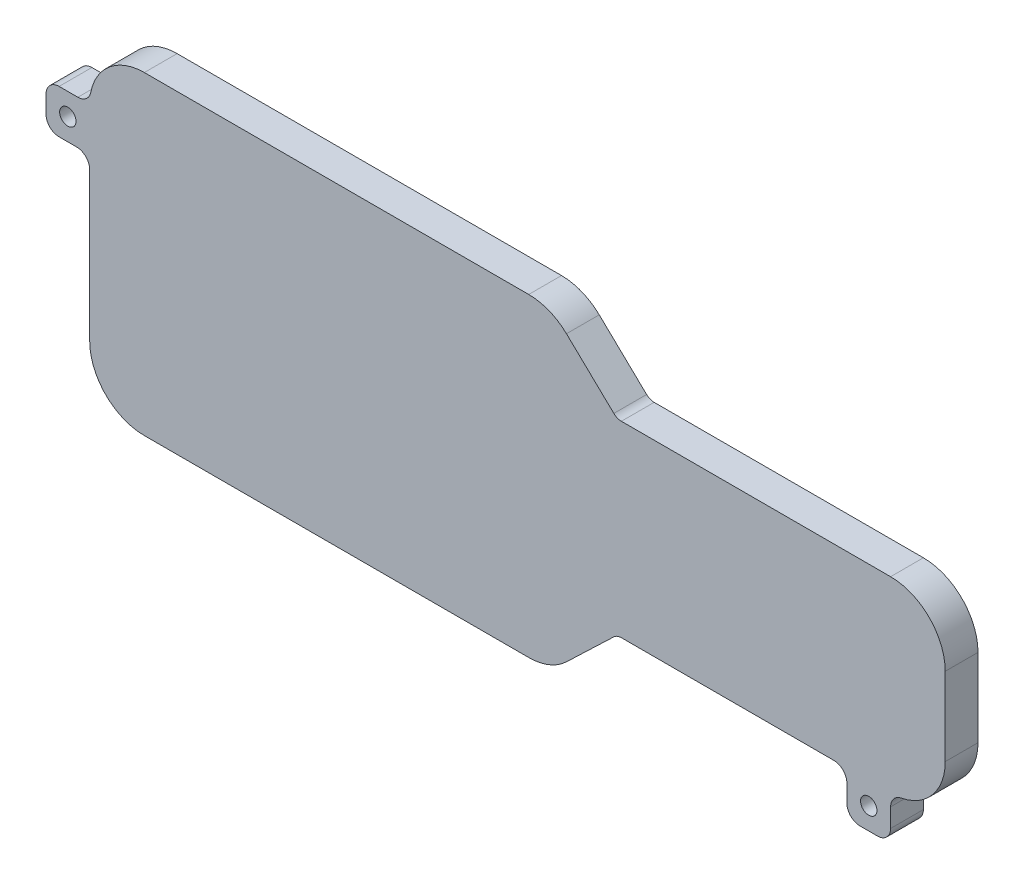
SolidWorks part; units mm, degrees
ref_plane "Front Plane" through (0, 0, 0) normal (0, 0, 1) x (1, 0, 0)
ref_plane "Top Plane" through (0, 0, 0) normal (0, 1, 0) x (1, 0, 0)
ref_plane "Right Plane" through (0, 0, 0) normal (1, 0, 0) x (0, 0, -1)
sketch "Sketch2" plane through (0, 0, 0) normal (0, 0, 1) x (1, 0, 0)
  line L0 (-34.29, 10.16) -> (0, 10.16)
  line L1 (-34.29, 10.16) -> (-34.29, 0)
  line L2 (-34.29, 0) -> (0, 0)
  line L3 (0, 10.16) -> (0, 0)
  line L4 (-69.31, 13.97) -> (-36.29, 13.97)
  line L5 (-69.31, 13.97) -> (-69.31, -3.81)
  line L6 (-69.31, -3.81) -> (-36.29, -3.81)
  line L7 (-36.29, 13.97) -> (-36.29, -3.81)
  line L8 (-31.29, 10.16) -> (-31.29, 0)
  line L9 (-71.31, 15.97) -> (-34.29, 15.97)
  line L10 (-34.29, 15.97) -> (-34.29, 12.16)
  line L11 (-34.29, 12.16) -> (-31.29, 12.16)
  line L12 (-31.29, 12.16) -> (-31.29, -2)
  line L13 (-31.29, -2) -> (-34.29, -2)
  line L14 (-34.29, -2) -> (-34.29, -5.81)
  line L15 (-34.29, -5.81) -> (-71.31, -5.81)
  line L16 (-71.31, -5.81) -> (-71.31, 15.97)
  point P4 (-34.29, 5.08)
  point P5 (-36.29, 5.08)
  dimension "D1" = 2
  dimension "D2" = 2
  dimension "D3" = 2
  dimension "D5" = 2
  dimension "D4" = 2
  dimension "D6" = 0
sketch "Sketch3" plane through (0, 0, 0) normal (0, 0, 1) x (1, 0, 0)
  line L0 (-69.81, 17.47) -> (-34.6251, 17.47)
  line L1 (-32.5518, 16.6383) -> (-28.2152, 12.4917)
  line L2 (-26.1419, 11.66) -> (-1.5, 11.66)
  line L3 (1.5, 8.66) -> (1.5, 1.5)
  line L4 (-1.5, -1.5) -> (-26.1419, -1.5)
  line L5 (-28.2152, -2.3317) -> (-32.5518, -6.4783)
  line L6 (-34.6251, -7.31) -> (-69.81, -7.31)
  line L7 (-72.81, -4.31) -> (-72.81, 14.47)
  line L8 (-71.31, 15.97) -> (-34.29, 15.97) construction
  line L9 (-34.29, -5.81) -> (-71.31, -5.81) construction
  line L11 (-34.29, 0) -> (0, 0) construction
  line L12 (0, 10.16) -> (0, 0) construction
  line L13 (-71.31, -5.81) -> (-71.31, 15.97) construction
  line L14 (-69.81, 19.47) -> (-34.6251, 19.47)
  line L15 (-31.1696, 18.0838) -> (-26.833, 13.9372)
  line L16 (-26.1419, 13.66) -> (-1.5, 13.66)
  line L17 (3.5, 8.66) -> (3.5, 1.5)
  line L18 (-1.5, -3.5) -> (-26.1419, -3.5)
  line L19 (-26.833, -3.7772) -> (-31.1696, -7.9238)
  line L20 (-34.6251, -9.31) -> (-69.81, -9.31)
  line L21 (-74.81, -4.31) -> (-74.81, 14.47)
  arc A0 (-69.81, -7.31) -> (-72.81, -4.31) centre (-69.81, -4.31) cw
  arc A1 (-1.5, 11.66) -> (1.5, 8.66) centre (-1.5, 8.66) cw
  arc A2 (1.5, 1.5) -> (-1.5, -1.5) centre (-1.5, 1.5) cw
  arc A3 (-32.5518, -6.4783) -> (-34.6251, -7.31) centre (-34.6251, -4.31) cw
  arc A4 (-26.1419, -1.5) -> (-28.2152, -2.3317) centre (-26.1419, -4.5) ccw
  arc A5 (-28.2152, 12.4917) -> (-26.1419, 11.66) centre (-26.1419, 14.66) ccw
  arc A6 (-34.6251, 17.47) -> (-32.5518, 16.6383) centre (-34.6251, 14.47) cw
  arc A7 (-69.81, 17.47) -> (-72.81, 14.47) centre (-69.81, 14.47) ccw
  arc A8 (-34.6251, 19.47) -> (-31.1696, 18.0838) centre (-34.6251, 14.47) cw
  arc A9 (-26.833, 13.9372) -> (-26.1419, 13.66) centre (-26.1419, 14.66) ccw
  arc A10 (-1.5, 13.66) -> (3.5, 8.66) centre (-1.5, 8.66) cw
  arc A11 (3.5, 1.5) -> (-1.5, -3.5) centre (-1.5, 1.5) cw
  arc A12 (-26.1419, -3.5) -> (-26.833, -3.7772) centre (-26.1419, -4.5) ccw
  arc A13 (-31.1696, -7.9238) -> (-34.6251, -9.31) centre (-34.6251, -4.31) cw
  arc A14 (-69.81, -9.31) -> (-74.81, -4.31) centre (-69.81, -4.31) cw
  arc A15 (-69.81, 19.47) -> (-74.81, 14.47) centre (-69.81, 14.47) ccw
  point P26 (-33.4216, -7.31)
  point P29 (-27.3454, -1.5)
  point P32 (-27.3454, 11.66)
  point P35 (-33.4216, 17.47)
  dimension "D5" = 3
  dimension "D1" = 1.5
  dimension "D2" = 1.5
  dimension "D3" = 1.5
  dimension "D4" = 1.5
extrude "Boss-Extrude2" add sketch "Sketch3" along normal blind 12 and the other way blind 3
sketch "Sketch5" plane through (0, 0, -3) normal (0, 0, -1) x (-1, 0, 0)
  line L0 (-1.5, 1.5) -> (-1.5, 8.66) construction
  line L1 (26.1419, -1.5) -> (1.5, -1.5) construction
  line L2 (32.5518, -6.4783) -> (28.2152, -2.3317) construction
  line L3 (69.81, -7.31) -> (34.6251, -7.31) construction
  line L4 (72.81, 14.47) -> (72.81, -4.31) construction
  line L5 (-1.5, 1.5) -> (-1.5, 8.66)
  line L6 (26.1419, -1.5) -> (1.5, -1.5)
  line L7 (32.5518, -6.4783) -> (28.2152, -2.3317)
  line L8 (72.81, -4.31) -> (72.81, 14.47)
  line L9 (34.6251, -7.31) -> (69.81, -7.31)
  line L10 (28.2152, -2.3317) -> (32.5518, -6.4783)
  line L11 (1.5, -1.5) -> (26.1419, -1.5)
  line L12 (-1.5, 8.66) -> (-1.5, 1.5)
  line L13 (26.1419, 11.66) -> (1.5, 11.66)
  line L14 (32.5518, 16.6383) -> (28.2152, 12.4917)
  line L15 (69.81, 17.47) -> (34.6251, 17.47)
  line L16 (72.81, -4.31) -> (72.81, 14.47)
  line L17 (34.6251, -7.31) -> (69.81, -7.31)
  line L18 (28.2152, -2.3317) -> (32.5518, -6.4783)
  line L19 (1.5, -1.5) -> (26.1419, -1.5)
  line L20 (-1.5, 8.66) -> (-1.5, 1.5)
  line L21 (26.1419, 11.66) -> (1.5, 11.66)
  line L22 (32.5518, 16.6383) -> (28.2152, 12.4917)
  line L23 (69.81, 17.47) -> (34.6251, 17.47)
  line L24 (69.81, -7.31) -> (34.6251, -7.31)
  line L25 (72.81, 14.47) -> (72.81, -4.31)
  arc A0 (1.5, 11.66) -> (-1.5, 8.66) centre (1.5, 8.66) ccw construction
  arc A1 (-1.5, 1.5) -> (1.5, -1.5) centre (1.5, 1.5) ccw construction
  arc A2 (28.2152, -2.3317) -> (26.1419, -1.5) centre (26.1419, -4.5) ccw construction
  arc A3 (32.5518, -6.4783) -> (34.6251, -7.31) centre (34.6251, -4.31) ccw construction
  arc A4 (69.81, -7.31) -> (72.81, -4.31) centre (69.81, -4.31) ccw construction
  arc A5 (72.81, 14.47) -> (69.81, 17.47) centre (69.81, 14.47) ccw construction
  arc A6 (1.5, 11.66) -> (-1.5, 8.66) centre (1.5, 8.66) ccw
  arc A7 (-1.5, 1.5) -> (1.5, -1.5) centre (1.5, 1.5) ccw
  arc A8 (69.81, -7.31) -> (72.81, -4.31) centre (69.81, -4.31) ccw
  arc A9 (32.5518, -6.4783) -> (34.6251, -7.31) centre (34.6251, -4.31) ccw
  arc A10 (28.2152, -2.3317) -> (26.1419, -1.5) centre (26.1419, -4.5) ccw
  arc A11 (-1.5, 1.5) -> (1.5, -1.5) centre (1.5, 1.5) ccw
  arc A12 (1.5, 11.66) -> (-1.5, 8.66) centre (1.5, 8.66) ccw
  arc A13 (26.1419, 11.66) -> (28.2152, 12.4917) centre (26.1419, 14.66) ccw
  arc A14 (34.6251, 17.47) -> (32.5518, 16.6383) centre (34.6251, 14.47) ccw
  arc A15 (72.81, 14.47) -> (69.81, 17.47) centre (69.81, 14.47) ccw
  arc A16 (69.81, -7.31) -> (72.81, -4.31) centre (69.81, -4.31) ccw
  arc A17 (32.5518, -6.4783) -> (34.6251, -7.31) centre (34.6251, -4.31) ccw
  arc A18 (28.2152, -2.3317) -> (26.1419, -1.5) centre (26.1419, -4.5) ccw
  arc A19 (-1.5, 1.5) -> (1.5, -1.5) centre (1.5, 1.5) ccw
  arc A20 (1.5, 11.66) -> (-1.5, 8.66) centre (1.5, 8.66) ccw
  arc A21 (26.1419, 11.66) -> (28.2152, 12.4917) centre (26.1419, 14.66) ccw
  arc A22 (34.6251, 17.47) -> (32.5518, 16.6383) centre (34.6251, 14.47) ccw
  arc A23 (72.81, 14.47) -> (69.81, 17.47) centre (69.81, 14.47) ccw
  arc A24 (28.2152, -2.3317) -> (26.1419, -1.5) centre (26.1419, -4.5) ccw
  arc A25 (32.5518, -6.4783) -> (34.6251, -7.31) centre (34.6251, -4.31) ccw
  arc A26 (69.81, -7.31) -> (72.81, -4.31) centre (69.81, -4.31) ccw
  arc A27 (72.81, 14.47) -> (69.81, 17.47) centre (69.81, 14.47) ccw
  line M17 (72.81, 14.47) -> (72.81, -4.31)
  arc M18 (72.81, -4.31) -> (69.81, -7.31) centre (69.81, -4.31) cw
  line M19 (69.81, -7.31) -> (34.6251, -7.31)
  arc M20 (34.6251, -7.31) -> (32.5518, -6.4783) centre (34.6251, -4.31) cw
  line M21 (32.5518, -6.4783) -> (28.2152, -2.3317)
  arc M22 (28.2152, -2.3317) -> (26.1419, -1.5) centre (26.1419, -4.5) ccw
  line M23 (26.1419, -1.5) -> (1.5, -1.5)
  arc M24 (1.5, -1.5) -> (-1.5, 1.5) centre (1.5, 1.5) cw
  line M25 (-1.5, 1.5) -> (-1.5, 8.66)
  arc M26 (-1.5, 8.66) -> (1.5, 11.66) centre (1.5, 8.66) cw
  line M27 (1.5, 11.66) -> (26.1419, 11.66)
  arc M28 (26.1419, 11.66) -> (28.2152, 12.4917) centre (26.1419, 14.66) ccw
  line M29 (28.2152, 12.4917) -> (32.5518, 16.6383)
  arc M30 (32.5518, 16.6383) -> (34.6251, 17.47) centre (34.6251, 14.47) cw
  line M31 (34.6251, 17.47) -> (69.81, 17.47)
  arc M32 (69.81, 17.47) -> (72.81, 14.47) centre (69.81, 14.47) cw
  dimension "D1" = 0
extrude "Boss-Extrude3" add sketch "Sketch5" against normal blind 3 contours M17 M32 M31 M30 M29 M28 M27 M26 M25 M24 M23 M22 M21 M20 M19 M18
sketch "Sketch8" plane through (0, 0, 12) normal (0, 0, 1) x (1, 0, 0)
  line L1 (-74.81, 14.47) -> (-78.81, 14.47)
  line L2 (-74.81, 14.47) -> (-74.81, 10.47)
  line L3 (-74.81, 10.47) -> (-78.81, 10.47)
  line L4 (-78.81, 14.47) -> (-78.81, 10.47)
  line L5 (-1.5, -3.5) -> (-5.5, -3.5)
  line L6 (-1.5, -3.5) -> (-1.5, -7.5)
  line L7 (-1.5, -7.5) -> (-5.5, -7.5)
  line L8 (-5.5, -3.5) -> (-5.5, -7.5)
  dimension "D1" = 4
extrude "Boss-Extrude4" add sketch "Sketch8" against normal through all
fillet "Fillet2" radius 1.2 8 edges at (-1.5, -3.5, 4.5) (-1.5, -7.5, 4.5) (-5.5, -7.5, 4.5) (-5.5, -3.5, 4.5) (-74.81, 14.47, 4.5) (-74.81, 10.47, 4.5) (-78.81, 14.47, 4.5) (-78.81, 10.47, 4.5)
sketch "Sketch9" plane through (0, 0, 12) normal (0, 0, 1) x (1, 0, 0)
  line L0 (-75.8928, 14.47) -> (-77.61, 14.47) construction
  line L1 (-78.81, 13.27) -> (-78.81, 11.67) construction
  line L2 (-4.3, -7.5) -> (-2.7, -7.5) construction
  line L3 (-5.5, -4.7) -> (-5.5, -6.3) construction
  circle A0 centre (-76.81, 12.47) radius 0.75
  circle A1 centre (-3.5, -5.5) radius 0.75
  dimension "D5" = 1.5
  dimension "D6" = 1.5
  dimension "D1" = 2
  dimension "D2" = 2
  dimension "D3" = 2
  dimension "D4" = 2
extrude "Cut-Extrude3" cut sketch "Sketch9" against normal through all
sketch "Sketch10" plane through (0, 0, -3) normal (0, 0, -1) x (-1, 0, 0)
  line L0 (34.6251, 19.47) -> (69.81, 19.47) construction
  line L1 (74.81, 9.27) -> (74.81, -4.31) construction
  circle A0 centre (62.81, 5.08) radius 3.5
  dimension "D3" = 7
  dimension "D1" = 14.39
  dimension "D2" = 12
extrude "Cut-Extrude4" cut sketch "Sketch10" against normal blind 1.5
fillet "Fillet3" radius 0.3 1 edges at (-66.31, 5.08, -3)
sketch "Sketch11" plane through (0, 0, 12) normal (0, 0, 1) x (1, 0, 0)
  line L10 (-69.81, -7.31) -> (-34.6251, -7.31)
  line L11 (-72.81, 14.47) -> (-72.81, -4.31)
  line L12 (-34.6251, 17.47) -> (-69.81, 17.47)
  line L13 (-28.2152, 12.4917) -> (-32.5518, 16.6383)
  line L14 (-1.5, 11.66) -> (-26.1419, 11.66)
  line L15 (1.5, 1.5) -> (1.5, 8.66)
  line L16 (-4.3, -7.5) -> (-2.7, -7.5)
  line L17 (-1.5, -6.3) -> (-1.5, -4.5828)
  line L18 (3.5, 1.5) -> (3.5, 8.66)
  line L19 (-1.5, 13.66) -> (-26.1419, 13.66)
  line L20 (-26.833, 13.9372) -> (-31.1696, 18.0838)
  line L21 (-34.6251, 19.47) -> (-69.81, 19.47)
  line L22 (-75.8928, 14.47) -> (-77.61, 14.47)
  line L23 (-78.81, 13.27) -> (-78.81, 11.67)
  line L24 (-77.61, 10.47) -> (-76.01, 10.47)
  line L25 (-74.81, 9.27) -> (-74.81, -4.31)
  line L26 (-69.81, -9.31) -> (-34.6251, -9.31)
  line L27 (-31.1696, -7.9238) -> (-26.833, -3.7772)
  line L28 (-26.1419, -3.5) -> (-6.7, -3.5)
  line L29 (-5.5, -4.7) -> (-5.5, -6.3)
  line L30 (-4.3, -7.5) -> (-2.7, -7.5)
  line L31 (-1.5, -6.3) -> (-1.5, -4.5828)
  line L32 (3.5, 1.5) -> (3.5, 8.66)
  line L33 (-1.5, 13.66) -> (-26.1419, 13.66)
  line L34 (-26.833, 13.9372) -> (-31.1696, 18.0838)
  line L35 (-34.6251, 19.47) -> (-69.81, 19.47)
  line L36 (-75.8928, 14.47) -> (-77.61, 14.47)
  line L37 (-78.81, 13.27) -> (-78.81, 11.67)
  line L38 (-77.61, 10.47) -> (-76.01, 10.47)
  line L39 (-74.81, 9.27) -> (-74.81, -4.31)
  line L40 (-69.81, -9.31) -> (-34.6251, -9.31)
  line L41 (-31.1696, -7.9238) -> (-26.833, -3.7772)
  line L42 (-26.1419, -3.5) -> (-6.7, -3.5)
  line L43 (-5.5, -4.7) -> (-5.5, -6.3)
  line L44 (-26.1419, -1.5) -> (-1.5, -1.5)
  line L45 (-32.5518, -6.4783) -> (-28.2152, -2.3317)
  line L46 (-69.81, -7.31) -> (-34.6251, -7.31)
  line L47 (-72.81, 14.47) -> (-72.81, -4.31)
  line L48 (-34.6251, 17.47) -> (-69.81, 17.47)
  line L49 (-28.2152, 12.4917) -> (-32.5518, 16.6383)
  line L50 (-1.5, 11.66) -> (-26.1419, 11.66)
  line L51 (1.5, 1.5) -> (1.5, 8.66)
  line L52 (-26.1419, -1.5) -> (-1.5, -1.5)
  line L53 (-32.5518, -6.4783) -> (-28.2152, -2.3317)
  arc A8 (-72.81, -4.31) -> (-69.81, -7.31) centre (-69.81, -4.31) ccw
  arc A9 (-69.81, 17.47) -> (-72.81, 14.47) centre (-69.81, 14.47) ccw
  arc A10 (-32.5518, 16.6383) -> (-34.6251, 17.47) centre (-34.6251, 14.47) ccw
  arc A11 (-28.2152, 12.4917) -> (-26.1419, 11.66) centre (-26.1419, 14.66) ccw
  arc A12 (1.5, 8.66) -> (-1.5, 11.66) centre (-1.5, 8.66) ccw
  arc A13 (-1.5, -1.5) -> (1.5, 1.5) centre (-1.5, 1.5) ccw
  arc A14 (-26.1419, -1.5) -> (-28.2152, -2.3317) centre (-26.1419, -4.5) ccw
  arc A15 (-34.6251, -7.31) -> (-32.5518, -6.4783) centre (-34.6251, -4.31) ccw
  arc A16 (-2.7, -7.5) -> (-1.5, -6.3) centre (-2.7, -6.3) ccw
  arc A17 (-0.5323, -3.4055) -> (-1.5, -4.5828) centre (-0.3, -4.5828) ccw
  arc A18 (-0.5323, -3.4055) -> (3.5, 1.5) centre (-1.5, 1.5) ccw
  arc A19 (3.5, 8.66) -> (-1.5, 13.66) centre (-1.5, 8.66) ccw
  arc A20 (-26.833, 13.9372) -> (-26.1419, 13.66) centre (-26.1419, 14.66) ccw
  arc A21 (-31.1696, 18.0838) -> (-34.6251, 19.47) centre (-34.6251, 14.47) ccw
  arc A22 (-69.81, 19.47) -> (-74.7155, 15.4377) centre (-69.81, 14.47) ccw
  arc A23 (-75.8928, 14.47) -> (-74.7155, 15.4377) centre (-75.8928, 15.67) ccw
  arc A24 (-77.61, 14.47) -> (-78.81, 13.27) centre (-77.61, 13.27) ccw
  arc A25 (-78.81, 11.67) -> (-77.61, 10.47) centre (-77.61, 11.67) ccw
  arc A26 (-74.81, 9.27) -> (-76.01, 10.47) centre (-76.01, 9.27) ccw
  arc A27 (-74.81, -4.31) -> (-69.81, -9.31) centre (-69.81, -4.31) ccw
  arc A28 (-34.6251, -9.31) -> (-31.1696, -7.9238) centre (-34.6251, -4.31) ccw
  arc A29 (-26.1419, -3.5) -> (-26.833, -3.7772) centre (-26.1419, -4.5) ccw
  arc A30 (-5.5, -4.7) -> (-6.7, -3.5) centre (-6.7, -4.7) ccw
  arc A31 (-5.5, -6.3) -> (-4.3, -7.5) centre (-4.3, -6.3) ccw
  arc A32 (-2.7, -7.5) -> (-1.5, -6.3) centre (-2.7, -6.3) ccw
  arc A33 (-0.5323, -3.4055) -> (-1.5, -4.5828) centre (-0.3, -4.5828) ccw
  arc A34 (-0.5323, -3.4055) -> (3.5, 1.5) centre (-1.5, 1.5) ccw
  arc A35 (3.5, 8.66) -> (-1.5, 13.66) centre (-1.5, 8.66) ccw
  arc A36 (-26.833, 13.9372) -> (-26.1419, 13.66) centre (-26.1419, 14.66) ccw
  arc A37 (-31.1696, 18.0838) -> (-34.6251, 19.47) centre (-34.6251, 14.47) ccw
  arc A38 (-69.81, 19.47) -> (-74.7155, 15.4377) centre (-69.81, 14.47) ccw
  arc A39 (-75.8928, 14.47) -> (-74.7155, 15.4377) centre (-75.8928, 15.67) ccw
  arc A40 (-77.61, 14.47) -> (-78.81, 13.27) centre (-77.61, 13.27) ccw
  arc A41 (-78.81, 11.67) -> (-77.61, 10.47) centre (-77.61, 11.67) ccw
  arc A42 (-74.81, 9.27) -> (-76.01, 10.47) centre (-76.01, 9.27) ccw
  arc A43 (-74.81, -4.31) -> (-69.81, -9.31) centre (-69.81, -4.31) ccw
  arc A44 (-34.6251, -9.31) -> (-31.1696, -7.9238) centre (-34.6251, -4.31) ccw
  arc A45 (-26.1419, -3.5) -> (-26.833, -3.7772) centre (-26.1419, -4.5) ccw
  arc A46 (-5.5, -4.7) -> (-6.7, -3.5) centre (-6.7, -4.7) ccw
  arc A47 (-5.5, -6.3) -> (-4.3, -7.5) centre (-4.3, -6.3) ccw
  arc A48 (-72.81, -4.31) -> (-69.81, -7.31) centre (-69.81, -4.31) ccw
  arc A49 (-69.81, 17.47) -> (-72.81, 14.47) centre (-69.81, 14.47) ccw
  arc A50 (-32.5518, 16.6383) -> (-34.6251, 17.47) centre (-34.6251, 14.47) ccw
  arc A51 (-28.2152, 12.4917) -> (-26.1419, 11.66) centre (-26.1419, 14.66) ccw
  arc A52 (1.5, 8.66) -> (-1.5, 11.66) centre (-1.5, 8.66) ccw
  arc A53 (-1.5, -1.5) -> (1.5, 1.5) centre (-1.5, 1.5) ccw
  arc A54 (-26.1419, -1.5) -> (-28.2152, -2.3317) centre (-26.1419, -4.5) ccw
  arc A55 (-34.6251, -7.31) -> (-32.5518, -6.4783) centre (-34.6251, -4.31) ccw
  dimension "D1" = 0
  dimension "D2" = 0
extrude "Cut-Extrude5" cut sketch "Sketch11" against normal blind 12
equation "\"D5@Sketch2\"=\"pcb_overflow\""
equation "\"D1@Sketch2\"=\"pcb_overflow\""
equation "\"D2@Sketch2\"=\"pcb_overflow\""
equation "\"D4@Sketch2\"=\"pcb_overflow\""
equation "\"D3@Sketch2\"=\"pcb_overflow\""
equation "\"D1@Sketch3\"=\"gap_from_case\""
equation "\"D2@Sketch3\"=\"gap_from_case\""
equation "\"D3@Sketch3\"=\"gap_from_case\""
equation "\"D4@Sketch3\"=\"gap_from_case\""
